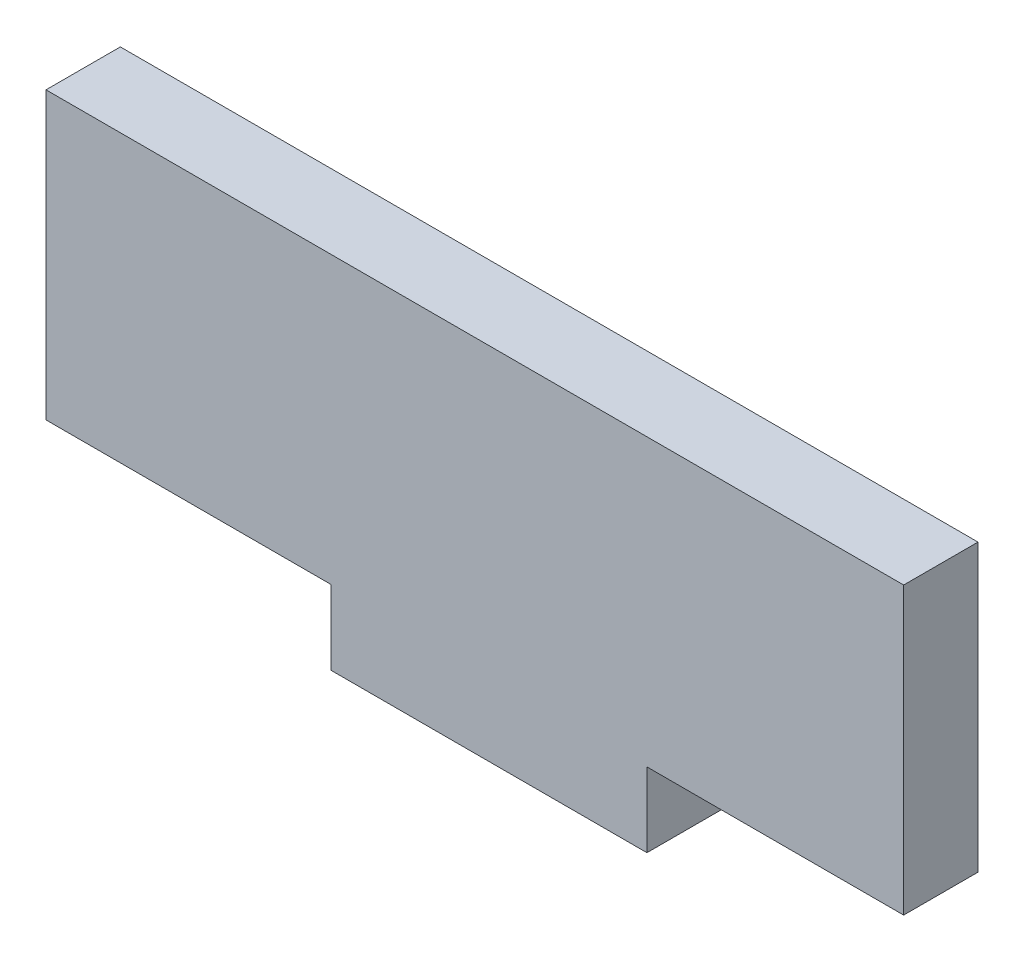
SolidWorks part; units mm, degrees
ref_plane "Front Plane" through (0, 0, 0) normal (0, 0, 1) x (1, 0, 0)
ref_plane "Top Plane" through (0, 0, 0) normal (0, 1, 0) x (1, 0, 0)
ref_plane "Right Plane" through (0, 0, 0) normal (1, 0, 0) x (0, 0, -1)
sketch "Sketch1" plane through (0, 0, 0) normal (0, 0, 1) x (1, 0, 0)
  line L0 (21.0202, 0) -> (30, 0)
  line L1 (0, 0) -> (9.9773, 0)
  line L2 (0, 0) -> (0, 10)
  line L3 (0, 10) -> (30, 10)
  line L4 (30, 0) -> (30, 10)
  line L6 (9.9773, 0) -> (9.9773, -2.6)
  line L7 (9.9773, -2.6) -> (21.0202, -2.6)
  line L8 (21.0202, 0) -> (21.0202, -2.6)
  dimension "D1" = 10
  dimension "D2" = 30
  dimension "D3" = 2.6
extrude "Boss-Extrude1" add sketch "Sketch1" along normal blind 2.6
equation "\"D3@Sketch1\" = \"mdf@fmv1.assembly\""
equation "\"D1@Boss-Extrude1\"=\"mdf@fmv1.assembly\""
